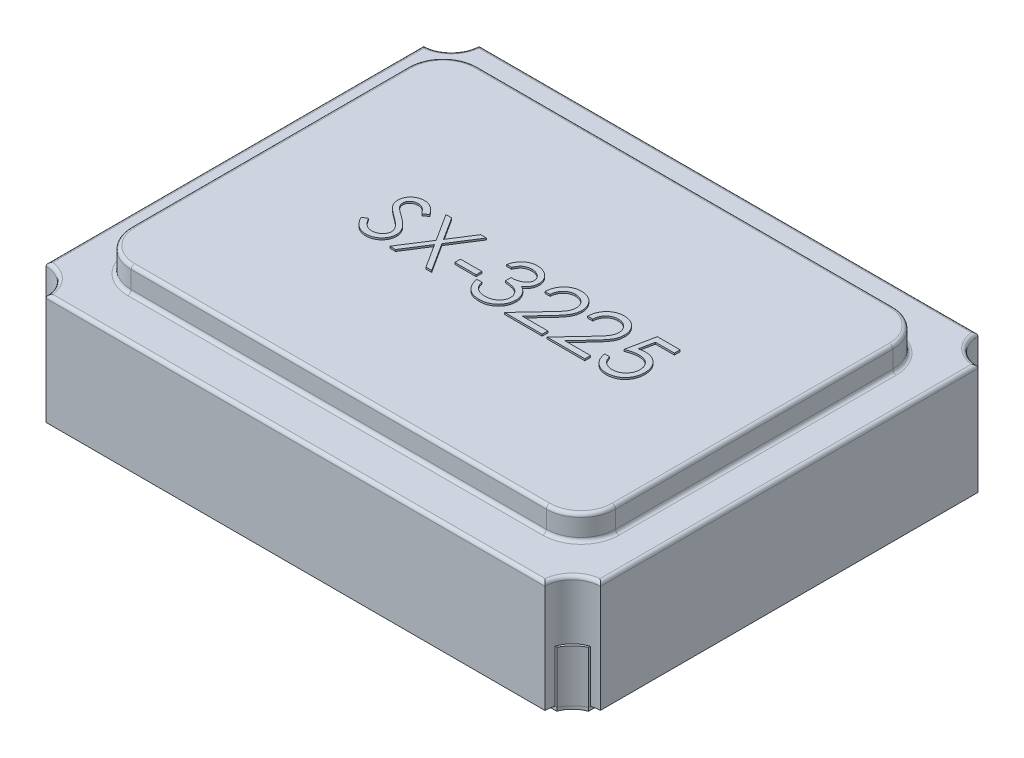
SolidWorks part; units mm, degrees
ref_plane "Спереди" through (0, 0, 0) normal (0, 0, 1) x (1, 0, 0)
ref_plane "Сверху" through (0, 0, 0) normal (0, 1, 0) x (1, 0, 0)
ref_plane "Справа" through (0, 0, 0) normal (1, 0, 0) x (0, 0, -1)
sketch "Эскиз2" plane through (0, 0, 0) normal (0, 1, 0) x (1, 0, 0)
  line L0 (0, -0.7737) -> (0, 0.9108) construction
  line L1 (1.7122, 0) -> (-1.6552, 0) construction
  line L2 (1.6, -1.25) -> (-1.6, -1.25) construction
  line L3 (1.6, -1.25) -> (1.6, 1.25) construction
  line L4 (1.6, 1.25) -> (-1.6, 1.25) construction
  line L5 (-1.6, -1.25) -> (-1.6, 1.25) construction
  line L6 (1.6, -1.25) -> (-1.6, 1.25) construction
  line L7 (1.6, 1.25) -> (-1.6, -1.25) construction
  line L8 (1.55, -1.2) -> (-1.55, -1.2) construction
  line L9 (1.55, -1.2) -> (1.55, 1.2) construction
  line L10 (1.55, 1.2) -> (-1.55, 1.2) construction
  line L11 (-1.55, -1.2) -> (-1.55, 1.2) construction
  line L12 (1.55, -1.2) -> (-1.55, 1.2) construction
  line L13 (1.55, 1.2) -> (-1.55, -1.2) construction
  line L14 (0.825, -1.25) -> (-0.825, -1.25) construction
  line L15 (0.825, -1.25) -> (0.825, 1.25) construction
  line L16 (0.825, 1.25) -> (-0.825, 1.25) construction
  line L17 (-0.825, -1.25) -> (-0.825, 1.25) construction
  line L18 (0.825, -1.25) -> (-0.825, 1.25) construction
  line L19 (0.825, 1.25) -> (-0.825, -1.25) construction
  line L20 (-1.4586, 1.2) -> (-0.825, 1.2)
  line L21 (-0.825, 1.2) -> (-0.825, 0.1984)
  line L22 (-0.825, -1.2) -> (-1.4586, -1.2)
  line L23 (-1.55, 1.1086) -> (-1.55, -1.1086)
  line L24 (1.55, 1.1086) -> (1.55, -1.1086)
  line L25 (0.825, -1.2) -> (1.4586, -1.2)
  line L26 (0.825, 1.2) -> (0.825, -1.2)
  line L27 (1.4586, 1.2) -> (0.825, 1.2)
  line L28 (-0.825, -0.1984) -> (-0.825, -1.2)
  circle A0 centre (-1.6, -1.25) radius 0.15 construction
  circle A1 centre (1.6, -1.25) radius 0.15 construction
  circle A2 centre (-1.6, 1.25) radius 0.15 construction
  circle A3 centre (1.6, 1.25) radius 0.15 construction
  arc A4 (-0.825, 0.1984) -> (-0.825, -0.1984) centre (-0.825, 0) cw
  arc A5 (-1.55, 1.1086) -> (-1.4586, 1.2) centre (-1.6, 1.25) ccw
  arc A6 (-1.55, -1.1086) -> (-1.4586, -1.2) centre (-1.6, -1.25) cw
  arc A7 (1.55, -1.1086) -> (1.4586, -1.2) centre (1.6, -1.25) ccw
  arc A8 (1.55, 1.1086) -> (1.4586, 1.2) centre (1.6, 1.25) cw
  point P2 (0, 0)
  point P9 (0, 0)
  point P20 (0, 0)
  dimension "D5" = 0.3
  dimension "D1" = 3.2
  dimension "D2" = 2.5
  dimension "D3" = 2
  dimension "D4" = 2
  dimension "D8" = 1.65
  dimension "D6" = 3.1
  dimension "D7" = 2
extrude "Бобышка-Вытянуть2" add sketch "Эскиз2" along normal blind 0.02
ref_plane "Плоскость1" through (0, 0.02, 0) normal (0, 1, 0) x (-1, 0, 0)
sketch "Эскиз5" plane through (0, 0.02, 0) normal (0, 1, 0) x (-1, 0, 0)
  line L0 (0, -0.8137) -> (0, 0.8285) construction
  line L1 (0.9756, 0) -> (-1.114, 0) construction
  line L2 (0.825, 1.2) -> (0.825, 0.1984) construction
  line L8 (1.4586, 1.2) -> (0.825, 1.2) construction
  line L9 (1.55, -1.1086) -> (1.55, 1.1086) construction
  line L10 (1.4586, 1.2) -> (1.4365, 1.2)
  line L11 (1.55, 1.1086) -> (1.55, 1.0865)
  line L12 (1.4586, -1.2) -> (1.4365, -1.2)
  line L13 (1.55, -1.1086) -> (1.55, -1.0865)
  line L14 (-1.4586, -1.2) -> (-1.4365, -1.2)
  line L15 (-1.55, -1.1086) -> (-1.55, -1.0865)
  line L16 (-1.55, 1.1086) -> (-1.55, 1.0865)
  line L17 (-1.4586, 1.2) -> (-1.4365, 1.2)
  arc A0 (1.55, 1.1086) -> (1.4586, 1.2) centre (1.6381, 1.2881) cw
  arc A1 (1.4365, 1.2) -> (1.55, 1.0865) centre (1.6381, 1.2881) ccw
  arc A2 (1.4365, -1.2) -> (1.55, -1.0865) centre (1.6381, -1.2881) cw
  arc A3 (1.55, -1.1086) -> (1.4586, -1.2) centre (1.6381, -1.2881) ccw
  arc A4 (-1.55, -1.1086) -> (-1.4586, -1.2) centre (-1.6381, -1.2881) cw
  arc A5 (-1.4365, -1.2) -> (-1.55, -1.0865) centre (-1.6381, -1.2881) ccw
  arc A6 (-1.55, 1.1086) -> (-1.4586, 1.2) centre (-1.6381, 1.2881) ccw
  arc A7 (-1.4365, 1.2) -> (-1.55, 1.0865) centre (-1.6381, 1.2881) cw
  dimension "D1" = 0.2
  dimension "D2" = 0.22
  dimension "D3" = 0
extrude "Бобышка-Вытянуть4" add sketch "Эскиз5" along normal blind 0.3
sketch "Эскиз6" plane through (0, 0.02, 0) normal (0, 1, 0) x (-1, 0, 0)
  line L0 (1.0415, 0) -> (-1.2862, 0) construction
  line L1 (-1.6, 1.25) -> (1.6, 1.25) construction
  line L2 (-1.6, 1.25) -> (-1.6, -1.25) construction
  line L3 (-1.6, -1.25) -> (1.6, -1.25) construction
  line L4 (1.6, 1.25) -> (1.6, -1.25) construction
  line L5 (-1.6, 1.25) -> (1.6, -1.25) construction
  line L6 (-1.6, -1.25) -> (1.6, 1.25) construction
  line L8 (0, -0.6677) -> (0, 1.0278) construction
  line L9 (1.44, -1.25) -> (-1.44, -1.25)
  line L10 (-1.6, -1.09) -> (-1.6, 1.09)
  line L13 (-1.44, 1.25) -> (1.44, 1.25)
  line L15 (1.6, 1.09) -> (1.6, -1.09)
  arc A0 (1.44, 1.25) -> (1.6, 1.09) centre (1.6, 1.25) ccw
  arc A2 (1.44, -1.25) -> (1.6, -1.09) centre (1.6, -1.25) cw
  arc A3 (-1.44, 1.25) -> (-1.6, 1.09) centre (-1.6, 1.25) cw
  arc A4 (-1.44, -1.25) -> (-1.6, -1.09) centre (-1.6, -1.25) ccw
  point P0 (0, 0)
  dimension "D3" = 0.16
  dimension "D1" = 3.2
  dimension "D2" = 2.5
extrude "Бобышка-Вытянуть8" add sketch "Эскиз6" along normal blind 0.64
ref_plane "Плоскость3" through (0, 0.66, 0) normal (0, 1, 0) x (-1, 0, 0)
sketch "Эскиз7" plane through (0, 0.66, 0) normal (0, 1, 0) x (-1, 0, 0)
  line L1 (-1.3979, 1) -> (1.3979, 1)
  line L2 (-1.3979, 1) -> (-1.3979, -1)
  line L3 (-1.3979, -1) -> (1.3979, -1)
  line L4 (1.3979, 1) -> (1.3979, -1)
  line L5 (-1.3979, 1) -> (1.3979, -1) construction
  line L6 (-1.3979, -1) -> (1.3979, 1) construction
  point P0 (0, 0)
  dimension "D1" = 2.7958
  dimension "D2" = 2
extrude "Бобышка-Вытянуть9" add sketch "Эскиз7" along normal blind 0.14
sketch "Эскиз8" plane through (0, 0.8, 0) normal (0, 1, 0) x (-1, 0, 0)
  line L0 (1.0732, 0.1668) -> (-1.1486, 0.1668) construction
  text T0 "SX-3225" font "Century Gothic" height 0.32
fillet "Скругление3" radius 0.2 4 edges at (1.3979, 0.73, -1) (1.3979, 0.73, 1) (-1.3979, 0.73, -1) (-1.3979, 0.73, 1)
fillet "Скругление4" radius 0.02 8 edges at (1.3393, 0.8, 0.9414) (0, 0.8, 1) (-1.3393, 0.8, 0.9414) (-1.3979, 0.8, 0) (-1.3393, 0.8, -0.9414) (0, 0.8, -1) (1.3393, 0.8, -0.9414) (1.3979, 0.8, 0)
fillet "Скругление5" radius 0.02 8 edges at (-1.3393, 0.66, 0.9414) (-1.3979, 0.66, 0) (-1.3393, 0.66, -0.9414) (0, 0.66, -1) (1.3393, 0.66, -0.9414) (1.3979, 0.66, 0) (1.3393, 0.66, 0.9414) (0, 0.66, 1)
fillet "Скругление6" radius 0.02 8 edges at (-1.6, 0.66, 0) (-1.4869, 0.66, -1.1369) (0, 0.66, -1.25) (1.4869, 0.66, -1.1369) (1.6, 0.66, 0) (1.4869, 0.66, 1.1369) (0, 0.66, 1.25) (-1.4869, 0.66, 1.1369)
extrude "Бобышка-Вытянуть10" add sketch "Эскиз8" along normal blind 0.01
